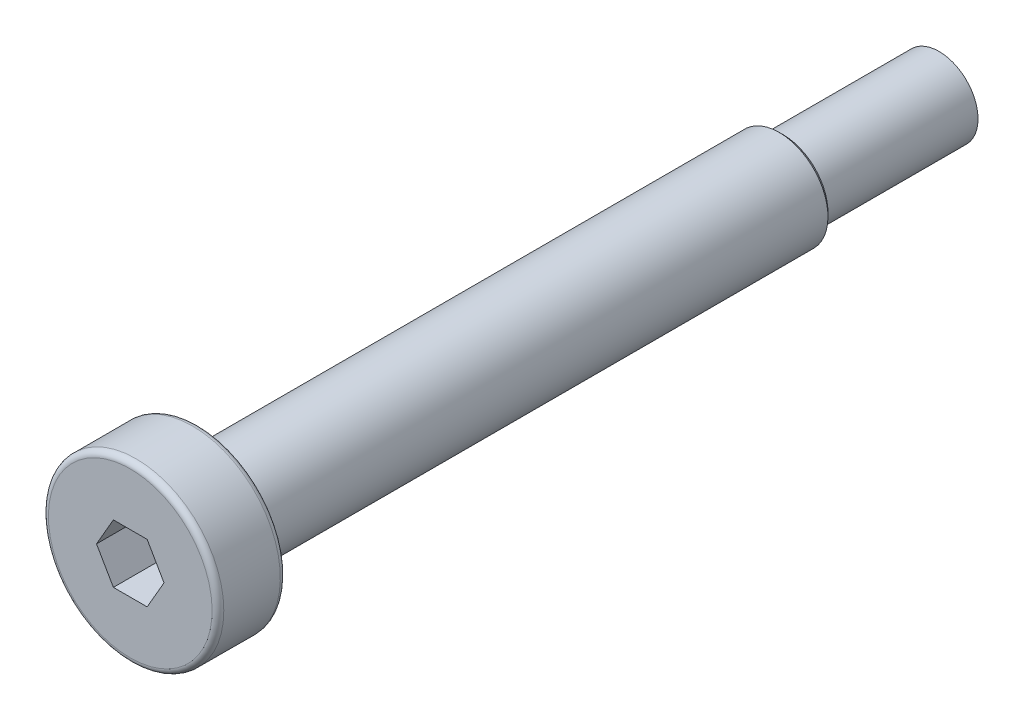
SolidWorks part; units mm, degrees
ref_plane "前视基准面" through (0, 0, 0) normal (0, 0, 1) x (1, 0, 0)
ref_plane "上视基准面" through (0, 0, 0) normal (0, 1, 0) x (1, 0, 0)
ref_plane "右视基准面" through (0, 0, 0) normal (1, 0, 0) x (0, 0, -1)
other "Configuration Table"
sketch "草图1" plane through (0, 0, 0) normal (1, 0, 0) x (0, 0, -1)
  line L0 (0, 0) -> (-41.5, 0) construction
  line L1 (0, 0) -> (0, 2)
  line L2 (0, 2) -> (-8, 2)
  line L3 (-8, 2) -> (-8, 2.5)
  line L4 (-8, 2.5) -> (-38, 2.5)
  line L5 (-38, 2.5) -> (-38, 4.5)
  line L6 (-38, 4.5) -> (-41.5, 4.5)
  line L7 (-41.5, 4.5) -> (-41.5, 0)
  line L8 (0, 0) -> (-41.5, 0)
  dimension "D1" = 4
  dimension "D2" = 5
  dimension "D3" = 8
  dimension "D4" = 9
  dimension "D5" = 3.5
  dimension "D6" = 30
revolve "旋转1" add sketch "草图1" angle 360 about L0
cosmetic thread "装饰螺纹线1"
fillet "圆角1" radius 0.3 2 edges at (0, 4.5, 38) (0, 4.5, 41.5)
sketch "草图2" plane through (0, 0, 41.5) normal (0, 0, 1) x (1, 0, 0)
  line L1 (1.7321, 0) -> (0.866, 1.5)
  line L2 (0.866, 1.5) -> (-0.866, 1.5)
  line L3 (-0.866, 1.5) -> (-1.7321, 0)
  line L4 (-1.7321, 0) -> (-0.866, -1.5)
  line L5 (-0.866, -1.5) -> (0.866, -1.5)
  line L6 (0.866, -1.5) -> (1.7321, 0)
  circle A0 centre (0, 0) radius 1.5 construction
  dimension "D1" = 3
extrude "切除-拉伸1" cut sketch "草图2" against normal blind 2.4
chamfer "倒角1" distance 0.2 angle 45 1 edges at (0, 2.5, 8)
